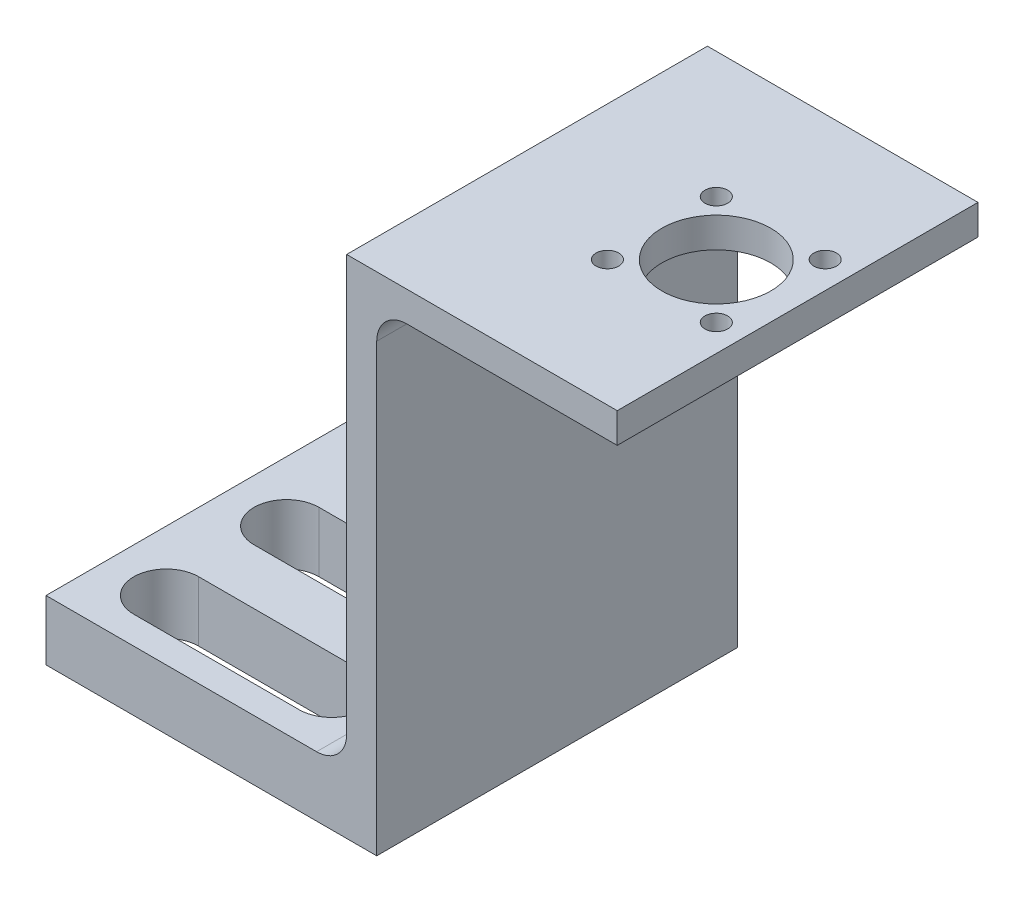
SolidWorks part; units mm, degrees
ref_plane "Front Plane" through (0, 0, 0) normal (0, 0, 1) x (1, 0, 0)
ref_plane "Top Plane" through (0, 0, 0) normal (0, 1, 0) x (1, 0, 0)
ref_plane "Right Plane" through (0, 0, 0) normal (1, 0, 0) x (0, 0, -1)
sketch "Sketch1" plane through (0, 0, 0) normal (0, 0, 1) x (1, 0, 0)
  line L0 (-34.925, 0) -> (0, 0)
  line L1 (0, 0) -> (0, 50.2412)
  line L2 (0, 50.2412) -> (25.4, 50.2412)
  line L3 (25.4, 50.2412) -> (25.4, 53.4162)
  line L4 (25.4, 53.4162) -> (-3.175, 53.4162)
  line L5 (-3.175, 53.4162) -> (-3.175, 6.35)
  line L6 (-3.175, 6.35) -> (-34.925, 6.35)
  line L7 (-34.925, 6.35) -> (-34.925, 0)
  line L9 (-941.2129, 25.908) -> (49058.7871, 25.908) construction
  point P3 (-3.175, 51.5271)
  dimension "D1" = 25.4
  dimension "D2" = 3.175
  dimension "D3" = 3.175
  dimension "D4" = 6.35
  dimension "D5" = 31.75
  dimension "D6" = 27.5082
  dimension "D7" = 25.908
extrude "Boss-Extrude1" add sketch "Sketch1" along normal mid plane 38.1
fillet "Fillet1" radius 3.175 2 edges at (0, 50.2412, 0) (-3.175, 6.35, 0)
extrude "Cut-Extrude1" cut sketch "Sketch2" against normal through all
sketch "Sketch2" plane through (16.8125, 50.2412, 0) normal (0, -1, 0) x (1, 0, 0)
  circle A0 centre (0, 0) radius 5.75
hole_wizard "M2 Clearance Hole1" positions "Sketch3" profile "Sketch4" hole size "M2" standard "ANSI Metric" end condition through all
sketch "Sketch3" plane through (16.8125, 50.2412, 0) normal (0, -1, 0) x (-1, 0, 0)
  point P0 (-5.75, -5.75)
  point P2 (-5.75, 5.75)
  point P4 (5.75, 5.75)
  point P6 (5.75, -5.75)
  point P9 (0, 0)
  point P12 (0, 0)
  point P15 (0, 0)
  point P18 (0, 0)
sketch "Sketch4" plane through (22.5625, 50.2412, 5.75) normal (1, 0, 0) x (0, 0, -1)
  line L0 (0, 0) -> (0, 3.175)
  line L1 (0, 3.175) -> (1.2, 3.175)
  line L2 (1.2, 3.175) -> (1.2, 0)
  line L3 (1.2, 0) -> (0, 0)
  line L4 (0, -6.35) -> (0, 107.95) construction
  dimension "Thru Hole Dia." = 2.4
  dimension "Thru Hole Depth" = 3.175
sketch "Sketch5" plane through (0, 6.35, 0) normal (0, 1, 0) x (1, 0, 0)
  line L0 (-28.575, 0) -> (-11.1125, 0) construction
  line L1 (-28.575, 3.429) -> (-11.1125, 3.429)
  line L2 (-28.575, -3.429) -> (-11.1125, -3.429)
  line L3 (-6.35, -19.05) -> (-6.35, 19.05) construction
  line L4 (-34.925, -19.05) -> (-34.925, 19.05) construction
  arc A0 (-28.575, 3.429) -> (-28.575, -3.429) centre (-28.575, 0) ccw
  arc A1 (-11.1125, -3.429) -> (-11.1125, 3.429) centre (-11.1125, 0) ccw
  point P3 (-19.8437, 0)
  dimension "D1" = 6.858
  dimension "D2" = 4.7625
  dimension "D3" = 6.35
extrude "Cut-Extrude2" cut sketch "Sketch5" against normal through all
pattern_linear "LPattern1" count 2 spacing 12.7 along (0, 0, 1) count 2 spacing 12.7 along (0, 0, -1) of "Cut-Extrude2"
